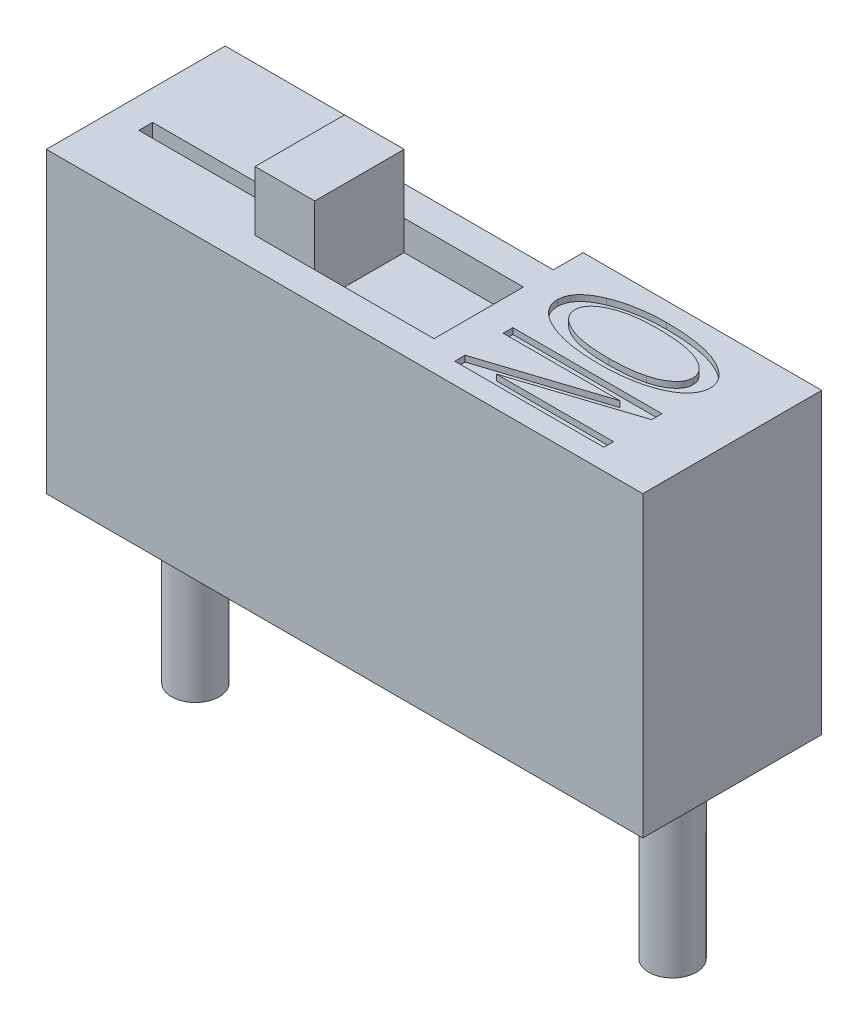
SolidWorks part; units mm, degrees
ref_plane "Plano frontal" through (0, 0, 0) normal (0, 0, 1) x (1, 0, 0)
ref_plane "Plano superior" through (0, 0, 0) normal (0, 1, 0) x (1, 0, 0)
ref_plane "Plano direito" through (0, 0, 0) normal (1, 0, 0) x (0, 0, -1)
sketch "Esboço1" plane through (0, 0, 0) normal (0, 1, 0) x (1, 0, 0)
  line L1 (0, 0) -> (10, 0)
  line L2 (0, 0) -> (0, 3)
  line L3 (0, 3) -> (10, 3)
  line L4 (10, 0) -> (10, 3)
  dimension "D1" = 3
  dimension "D2" = 10
extrude "Ressalto-extrusão1" add sketch "Esboço1" along normal blind 5 contours L3 L4 L1 L2
sketch "Esboço4" plane through (0, 5, 0) normal (0, 1, 0) x (1, 0, 0)
  line L1 (4, 2) -> (6.0031, 2)
  line L6 (4, 0.5) -> (3, 0.5)
  line L7 (4, 0.5) -> (4, 2)
  line L8 (4, 2) -> (3, 2)
  line L9 (3, 0.5) -> (3, 2)
  line L10 (4, 2) -> (4, 0.5)
  line L11 (4, 0.5) -> (6.0031, 0.5)
  line L12 (6.0031, 2) -> (6.0031, 0.5)
extrude "Ressalto-extrusão2" add sketch "Esboço4" along normal blind 1 contours L7 L6 L9 L8
sketch "Esboço8" plane through (0, 5, 0) normal (0, 1, 0) x (1, 0, 0)
  line L1 (4, 2) -> (6, 2)
  line L2 (4, 2) -> (4, 0.5)
  line L3 (4, 0.5) -> (6, 0.5)
  line L4 (6, 2) -> (6, 0.5)
  dimension "D1" = 1.5
  dimension "D2" = 2
extrude "Corte-extrusão2" cut sketch "Esboço8" against normal blind 0.5
sketch "Esboço9" plane through (0, 5, 0) normal (0, 1, 0) x (1, 0, 0)
  line L0 (6.5, 3) -> (6.5, 0) construction
  line L1 (0, 3) -> (10, 3) construction
  line L2 (0, 0) -> (10, 0) construction
  line L3 (6, 0.5) -> (6, 2) construction
  text T0 "ON" font "Arial Narrow" height 2.5
  dimension "D1" = 0.5
extrude "Corte-extrusão5" cut sketch "Esboço9" against normal blind 0.1
sketch "Esboço10" plane through (0, 5, 0) normal (0, 1, 0) x (1, 0, 0)
  line L0 (0.5, 3) -> (0.5, 0) construction
  line L1 (0, 3) -> (10, 3) construction
  line L2 (0, 0) -> (10, 0) construction
  line L3 (0, 0) -> (0, 3) construction
  text T0 " 1 " font "Century Gothic" height 2
  dimension "D1" = 0.5
extrude "Corte-extrusão6" cut sketch "Esboço10" against normal blind 0.5
sketch "Esboço11" plane through (0, 0, 0) normal (0, -1, 0) x (1, 0, 0)
  line L0 (0, -3) -> (1, -3)
  line L2 (0, -3) -> (10, -3) construction
  circle A0 centre (1, -1.5) radius 0.4
  circle A1 centre (9, -1.5) radius 0.4
  dimension "D3" = 0.8
  dimension "D4" = 0.8
  dimension "D1" = 1
extrude "Ressalto-extrusão4" add sketch "Esboço11" along normal blind 3 contours A0 | A1
sketch "Esboço19" plane through (0, 0, -3) normal (0, 0, -1) x (-1, 0, 0)
  line L0 (0, 5) -> (-3, 5)
  line L1 (0, 5) -> (-10, 5) construction
  line L3 (-3, 5) -> (-6, 5)
  line L4 (-3, 5) -> (-3, 3)
  line L5 (-3, 3) -> (-6, 3)
  line L6 (-6, 5) -> (-6, 3)
  dimension "D1" = 3
  dimension "D2" = 3
  dimension "D3" = 2
extrude "Corte-extrusão9" cut sketch "Esboço19" against normal blind 0.5
sketch "Esboço21" plane through (0, 0, -3) normal (0, 0, -1) x (-1, 0, 0)
  line L1 (-6, 3) -> (-3.0045, 3)
  line L2 (-6, 3) -> (-6, 2)
  line L3 (-6, 2) -> (-3.0045, 2)
  line L4 (-3.0045, 3) -> (-3.0045, 2)
  dimension "D1" = 1
extrude "Corte-extrusão10" cut sketch "Esboço21" against normal blind 0.3
